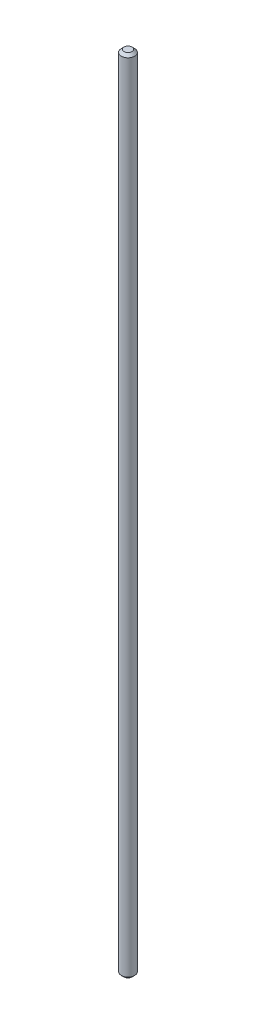
SolidWorks part; units mm, degrees
material "Alliage 1060"
ref_plane "Plan de face" through (0, 0, 0) normal (0, 0, 1) x (1, 0, 0)
ref_plane "Plan de dessus" through (0, 0, 0) normal (0, 1, 0) x (1, 0, 0)
ref_plane "Plan de droite" through (0, 0, 0) normal (1, 0, 0) x (0, 0, -1)
sketch "Esquisse1" plane through (0, 0, 0) normal (0, 1, 0) x (1, 0, 0)
  circle A0 centre (0, 0) radius 2.5
  dimension "D1" = 5
extrude "Boss.-Extru.1" add sketch "Esquisse1" along normal blind 300
chamfer "Chanfrein1" distance 1 angle 45 2 edges at (0, 0, 2.5) (0, 300, 2.5)
